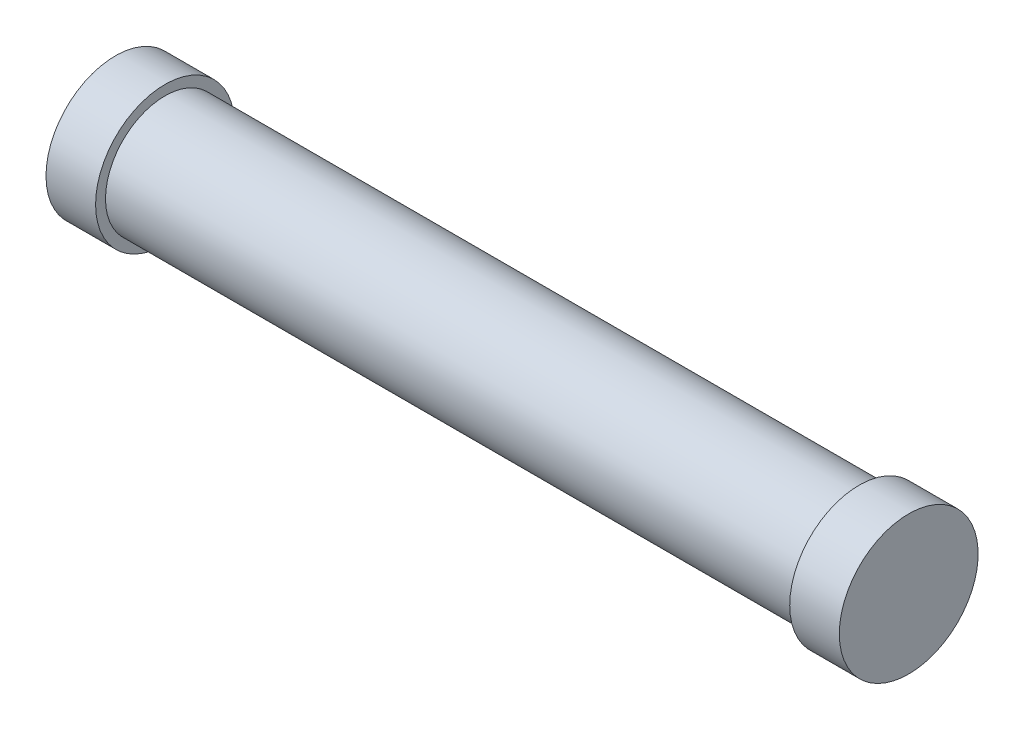
SolidWorks part; units mm, degrees
ref_plane "Front Plane" through (0, 0, 0) normal (0, 0, 1) x (1, 0, 0)
ref_plane "Top Plane" through (0, 0, 0) normal (0, 1, 0) x (1, 0, 0)
ref_plane "Right Plane" through (0, 0, 0) normal (1, 0, 0) x (0, 0, -1)
sketch "Sketch1" plane through (0, 0, 0) normal (0, 1, 0) x (1, 0, 0)
  line L2 (35.2795, 6) -> (35.2795, 12)
  line L3 (35.2795, 12) -> (-34.7205, 12)
  line L4 (-34.7205, 6) -> (-34.7205, 12)
  line L5 (0, 0) -> (-34.7205, 12) construction
  line L6 (35.2795, 12) -> (0, 0) construction
  line L7 (-34.7205, 6) -> (35.2795, 6) construction
  line L8 (-34.7205, 6) -> (35.2795, 6)
  point P0 (0, 0)
  dimension "D1" = 6
  dimension "D2" = 70
revolve "Revolve1" add sketch "Sketch1" angle 360 about L8
sketch "Sketch2" plane through (-34.7205, 0, 0) normal (-1, 0, 0) x (0, 0, 1)
  circle A0 centre (-6, 0) radius 7
extrude "Boss-Extrude1" add sketch "Sketch2" along normal blind 5
ref_plane "Plane1" through (0.2795, 0, 0) normal (1, 0, 0) x (0, 0, -1)
mirror "Mirror1" about plane through (0.2795, 0, 0) normal (1, 0, 0) of "Boss-Extrude1"
